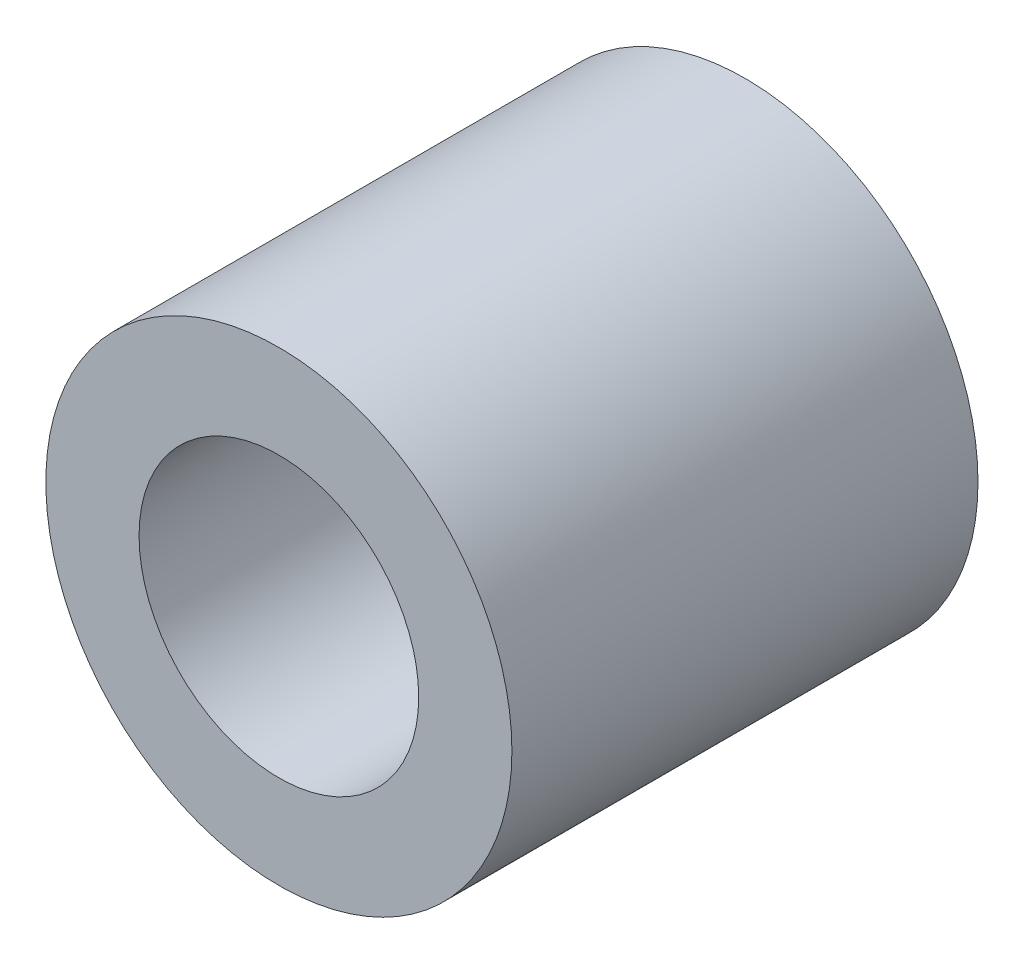
SolidWorks part; units mm, degrees
material "Delrin 2700 NC010, Low Viscosity Acetal Copolymer (SS)"
ref_plane "Front Plane" through (0, 0, 0) normal (0, 0, 1) x (1, 0, 0)
ref_plane "Top Plane" through (0, 0, 0) normal (0, 1, 0) x (1, 0, 0)
ref_plane "Right Plane" through (0, 0, 0) normal (1, 0, 0) x (0, 0, -1)
sketch "Sketch1" plane through (0, 0, 0) normal (0, 0, 1) x (1, 0, 0)
  circle A0 centre (0, 0) radius 3
  circle A1 centre (0, 0) radius 5
  dimension "D1" = 6
  dimension "D2" = 2
extrude "Boss-Extrude1" add sketch "Sketch1" along normal blind 10
